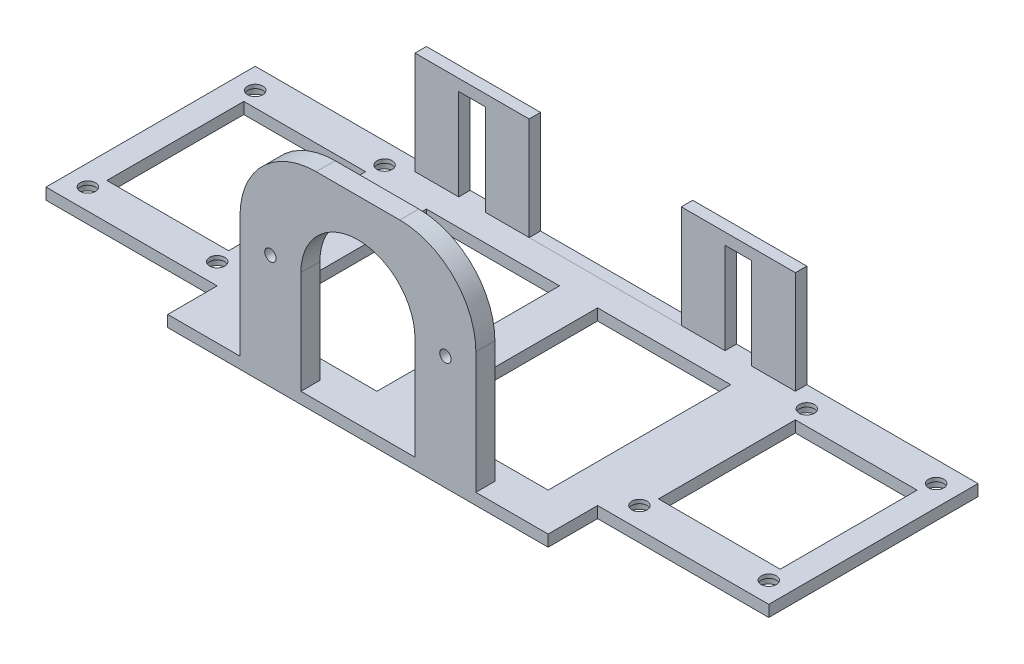
SolidWorks part; units mm, degrees
ref_plane "정면" through (0, 0, 0) normal (0, 0, 1) x (1, 0, 0)
ref_plane "윗면" through (0, 0, 0) normal (0, 1, 0) x (1, 0, 0)
ref_plane "우측면" through (0, 0, 0) normal (1, 0, 0) x (0, 0, -1)
sketch "스케치1" plane through (0, 0, 0) normal (0, 1, 0) x (1, 0, 0)
  line L1 (-50, 34) -> (50, 34)
  line L2 (-50, 34) -> (-50, -34)
  line L3 (-50, -34) -> (50, -34)
  line L4 (50, 34) -> (50, -34)
  line L5 (-50, 34) -> (50, -34) construction
  line L6 (-50, -34) -> (50, 34) construction
  point P0 (0, 0)
  dimension "D1" = 100
  dimension "D2" = 68
extrude "보스-돌출1" add sketch "스케치1" along normal blind 3
sketch "스케치2" plane through (0, 3, 0) normal (0, 1, 0) x (1, 0, 0)
  line L0 (-50, 34) -> (-50, -34) construction
  line L1 (50, 34) -> (-50, 34)
  line L2 (50, 34) -> (50, 31)
  line L3 (50, 31) -> (-50, 31)
  line L4 (-50, 34) -> (-50, 31)
  dimension "D1" = 3
extrude "보스-돌출2" add sketch "스케치2" along normal blind 27
sketch "스케치3" plane through (0, 0, -31) normal (0, 0, 1) x (1, 0, 0)
  line L0 (-50, 3) -> (50, 3) construction
  line L1 (-38.5, 27) -> (-31.5, 27)
  line L2 (-38.5, 27) -> (-38.5, 3)
  line L3 (-38.5, 3) -> (-31.5, 3)
  line L4 (-31.5, 27) -> (-31.5, 3)
  line L5 (-50, 30) -> (-50, 3) construction
  line L6 (-50, 3) -> (50, 3) construction
  line L7 (31.5, 27) -> (38.5, 27)
  line L8 (31.5, 27) -> (31.5, 3)
  line L9 (31.5, 3) -> (38.5, 3)
  line L10 (38.5, 27) -> (38.5, 3)
  line L11 (50, 30) -> (50, 3) construction
  dimension "D1" = 24
  dimension "D2" = 11.5
  dimension "D3" = 7
  dimension "D4" = 7
  dimension "D5" = 24
  dimension "D6" = 11.5
extrude "컷-돌출2" cut sketch "스케치3" against normal blind 27
sketch "스케치4" plane through (0, 3, 0) normal (0, 1, 0) x (1, 0, 0)
  line L0 (-50, -34) -> (50, -34) construction
  line L1 (-31, -29) -> (31, -29)
  line L2 (-31, -29) -> (-31, -34)
  line L3 (-31, -34) -> (31, -34)
  line L4 (31, -29) -> (31, -34)
  line L5 (50, -34) -> (50, 31) construction
  dimension "D1" = 5
  dimension "D2" = 62
  dimension "D3" = 19
extrude "보스-돌출3" add sketch "스케치4" along normal blind 52 contours L1 L4 L3 L2
sketch "스케치5" plane through (0, 0, 34) normal (0, 0, 1) x (1, 0, 0)
  line L0 (0, 55) -> (0, 0) construction
  line L1 (-50, 0) -> (50, 0) construction
  line L2 (-31, 55) -> (31, 55) construction
  line L3 (-15, 30) -> (-15, 3)
  line L4 (-15, 3) -> (15, 3)
  line L5 (15, 3) -> (15, 30)
  arc A0 (15, 30) -> (-15, 30) centre (0, 30) ccw
  circle A1 centre (-23, 30) radius 1.5
  circle A2 centre (23, 30) radius 1.5
  point P6 (0, 30)
  dimension "D2" = 15
  dimension "D4" = 3
  dimension "D7" = 23
  dimension "D1" = 30
  dimension "D3" = 3
  dimension "D5" = 23
  dimension "D6" = 30
  dimension "D8" = 15
  dimension "D9" = 15
extrude "컷-돌출4" cut sketch "스케치5" against normal blind 5
sketch "스케치7" plane through (0, 0, 0) normal (0, -1, 0) x (1, 0, 0)
  line L0 (50, 34) -> (50, -34) construction
  line L1 (40, 24) -> (5, 24)
  line L2 (40, 24) -> (40, -24)
  line L3 (40, -24) -> (5, -24)
  line L4 (5, 24) -> (5, -24)
  line L5 (50, -34) -> (-50, -34) construction
  line L6 (-50, 34) -> (50, 34) construction
  line L7 (-50, -34) -> (-50, 34) construction
  line L8 (-5, 24) -> (-40, 24)
  line L9 (-5, 24) -> (-5, -24)
  line L10 (-5, -24) -> (-40, -24)
  line L11 (-40, 24) -> (-40, -24)
  dimension "D1" = 10
  dimension "D2" = 10
  dimension "D3" = 10
  dimension "D4" = 10
  dimension "D5" = 10
  dimension "D6" = 10
  dimension "D7" = 5
  dimension "D8" = 5
extrude "컷-돌출5" cut sketch "스케치7" against normal blind 3
sketch "스케치8" plane through (50, 0, 0) normal (1, 0, 0) x (0, 0, -1)
  line L0 (-34, 3) -> (31, 3) construction
  line L1 (34, 0) -> (-21, 0)
  line L2 (34, 0) -> (34, 3)
  line L3 (34, 3) -> (-21, 3)
  line L4 (-21, 0) -> (-21, 3)
  dimension "D1" = 55
extrude "보스-돌출4" add sketch "스케치8" along normal blind 45
sketch "스케치11" plane through (-50, 0, 0) normal (-1, 0, 0) x (0, 0, 1)
  line L0 (-31, 3) -> (34, 3) construction
  line L1 (-34, 0) -> (21, 0)
  line L2 (-34, 0) -> (-34, 3)
  line L3 (-34, 3) -> (21, 3)
  line L4 (21, 0) -> (21, 3)
  dimension "D1" = 55
extrude "보스-돌출5" add sketch "스케치11" along normal blind 45
sketch "스케치10" plane through (0, 3, 0) normal (0, 1, 0) x (1, 0, 0)
  line L0 (95, -21) -> (50, -21) construction
  line L1 (52.5, -18.5) -> (92.5, -18.5) construction
  line L2 (52.5, -18.5) -> (52.5, 31.5) construction
  line L3 (52.5, 31.5) -> (92.5, 31.5) construction
  line L4 (92.5, -18.5) -> (92.5, 31.5) construction
  line L5 (95, 34) -> (95, -21) construction
  line L6 (52.5, 6.5) -> (92.5, 6.5) construction
  line L7 (72.5, -18.5) -> (72.5, 31.5) construction
  line L8 (0, -34) -> (0, 34) construction
  line L9 (50, 34) -> (-50, 34) construction
  line L11 (88.5, -11.5) -> (56.5, -11.5)
  line L12 (88.5, -11.5) -> (88.5, 24.5)
  line L13 (88.5, 24.5) -> (56.5, 24.5)
  line L14 (56.5, -11.5) -> (56.5, 24.5)
  line L15 (-88.5, 24.5) -> (-56.5, 24.5)
  line L16 (-56.5, -11.5) -> (-56.5, 24.5)
  line L17 (-88.5, -11.5) -> (-88.5, 24.5)
  line L18 (-88.5, -11.5) -> (-56.5, -11.5)
  circle A0 centre (55.5, -15.5) radius 2
  circle A1 centre (55.5, 28.5) radius 2
  circle A2 centre (89.5, 28.5) radius 2
  circle A3 centre (89.5, -15.5) radius 2
  circle A4 centre (-89.5, -15.5) radius 2
  circle A5 centre (-55.5, -15.5) radius 2
  circle A6 centre (-55.5, 28.5) radius 2
  circle A7 centre (-89.5, 28.5) radius 2
  dimension "D1" = 4
  dimension "D2" = 4
  dimension "D3" = 4
  dimension "D4" = 7
  dimension "D10" = 3
  dimension "D11" = 7
  dimension "D5" = 50
  dimension "D6" = 40
  dimension "D7" = 2.5
  dimension "D8" = 2.5
  dimension "D9" = 3
extrude "컷-돌출6" cut sketch "스케치10" against normal blind 45
sketch "스케치12" plane through (0, 0, 0) normal (0, -1, 0) x (1, 0, 0)
  line L0 (0, -34) -> (0, 34) construction
  line L1 (89.5, -28.5) -> (55.5, -28.5) construction
  line L2 (89.5, -28.5) -> (89.5, 15.5) construction
  line L3 (89.5, 15.5) -> (55.5, 15.5) construction
  line L4 (55.5, -28.5) -> (55.5, 15.5) construction
  line L5 (95, -34) -> (-95, -34) construction
  circle A0 centre (89.5, -28.5) radius 3
  circle A1 centre (89.5, 15.5) radius 3
  circle A2 centre (55.5, 15.5) radius 3
  circle A3 centre (55.5, -28.5) radius 3
  circle A4 centre (-89.5, 15.5) radius 3
  circle A5 centre (-55.5, 15.5) radius 3
  circle A6 centre (-55.5, -28.5) radius 3
  circle A7 centre (-89.5, -28.5) radius 3
  dimension "D1" = 6
  dimension "D2" = 6
  dimension "D3" = 6
  dimension "D4" = 6
extrude "컷-돌출7" cut sketch "스케치12" against normal blind 2
sketch "스케치13" plane through (0, 0, -34) normal (0, 0, -1) x (-1, 0, 0)
  line L2 (-50, 30) -> (50, 30) construction
  line L4 (-20, 30) -> (20, 30)
  line L5 (-20, 30) -> (-20, 2.9956)
  line L6 (-20, 2.9956) -> (20, 2.9956)
  line L12 (20, 30) -> (20, 2.9956)
  line L13 (-95, 0) -> (95, 0) construction
  line L14 (-31.5, 27) -> (-31.5, 3) construction
  line L15 (31.5, 3) -> (31.5, 27) construction
  dimension "D1" = 2.9956
  dimension "D2" = 11.5
  dimension "D3" = 11.5
extrude "컷-돌출8" cut sketch "스케치13" against normal blind 3
fillet "필렛1" radius 20 2 edges at (31, 55, 31.5) (-31, 55, 31.5)
